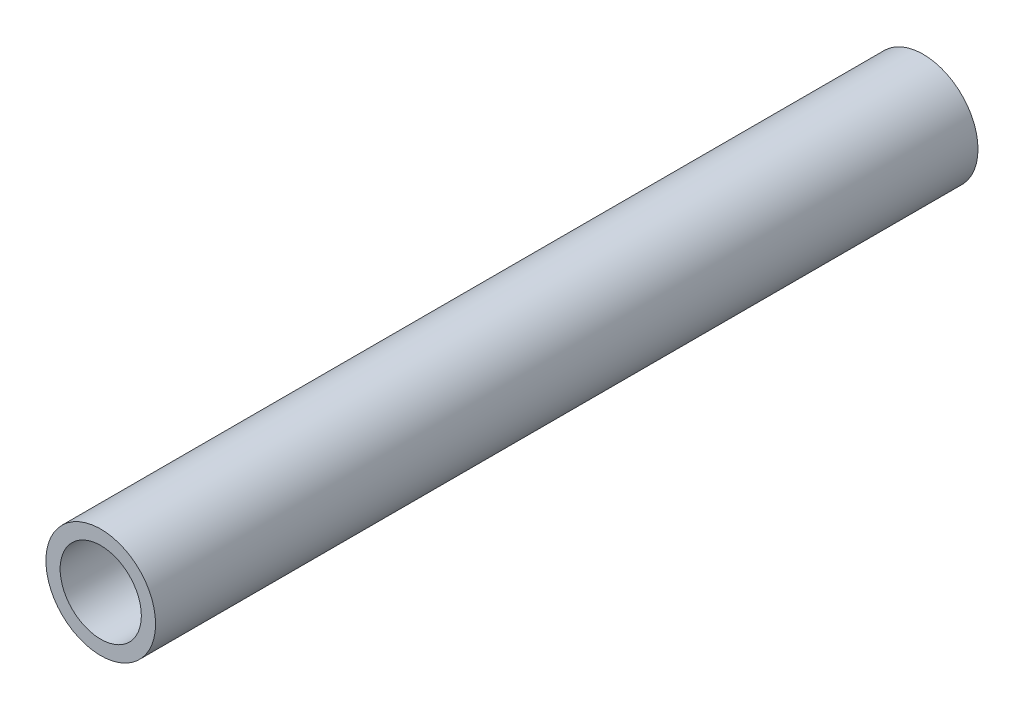
SolidWorks part; units mm, degrees
ref_plane "Front Plane" through (0, 0, 0) normal (0, 0, 1) x (1, 0, 0)
ref_plane "Top Plane" through (0, 0, 0) normal (0, 1, 0) x (1, 0, 0)
ref_plane "Right Plane" through (0, 0, 0) normal (1, 0, 0) x (0, 0, -1)
sketch "Sketch1" plane through (0, 0, 0) normal (0, 0, 1) x (1, 0, 0)
  circle A0 centre (0, 0) radius 10.668
  dimension "Pipe OD" = 21.336
extrude "Extrude-Thin1" add sketch "Sketch1" along normal mid plane 160 thin thin type one direction reverse wall 2.7686
